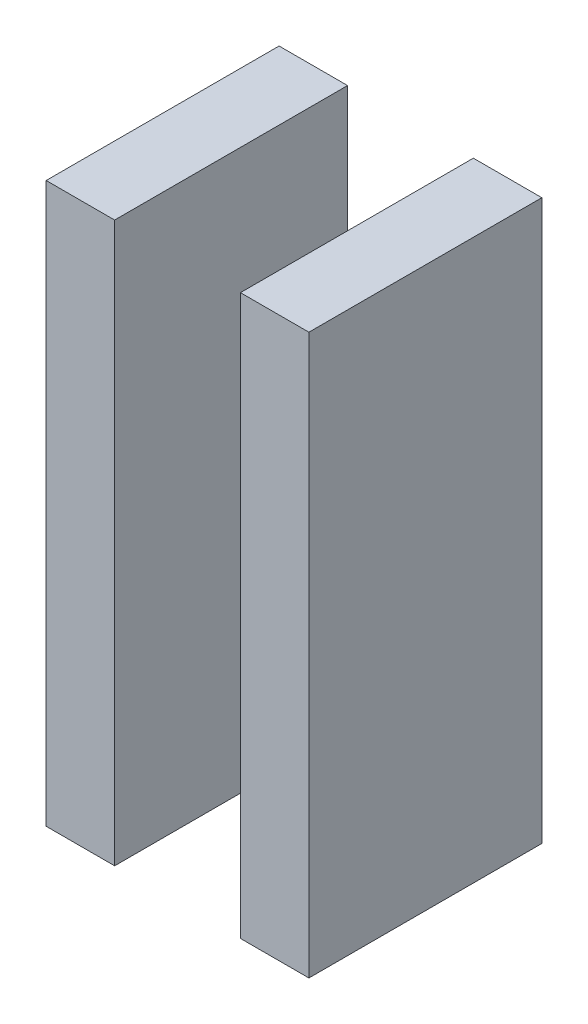
SolidWorks part; units mm, degrees
ref_plane "Ebene vorne" through (0, 0, 0) normal (0, 0, 1) x (1, 0, 0)
ref_plane "Ebene oben" through (0, 0, 0) normal (0, 1, 0) x (1, 0, 0)
ref_plane "Ebene rechts" through (0, 0, 0) normal (1, 0, 0) x (0, 0, -1)
sketch "Skizze1" plane through (0, 0, 0) normal (0, 0, 1) x (1, 0, 0)
  line L0 (194.515, -34.095) -> (192.485, -34.095) construction
  line L1 (192.03, -34.095) -> (194.97, -34.095)
  line L2 (192.03, -34.095) -> (192.03, -58.105)
  line L3 (192.03, -58.105) -> (194.97, -58.105)
  line L4 (194.97, -34.095) -> (194.97, -58.105)
  line L9 (192.485, -58.105) -> (194.515, -58.105) construction
  line L10 (197.67, -33.2751) -> (197.67, -43.9806) construction
  line L11 (200.37, -34.095) -> (200.37, -58.105)
  line L12 (203.31, -58.105) -> (200.37, -58.105)
  line L13 (203.31, -34.095) -> (203.31, -58.105)
  line L14 (203.31, -34.095) -> (200.37, -34.095)
  arc A0 (192.485, -34.095) -> (192.485, -35.005) centre (192.485, -34.55) ccw construction
  arc A1 (194.515, -39.705) -> (194.515, -38.795) centre (194.515, -39.25) ccw construction
  arc A2 (203.765, -35.005) -> (203.765, -34.095) centre (203.765, -34.55) ccw construction
extrude "Aufsatz-Linear austragen1" add sketch "Skizze1" along normal blind 10
